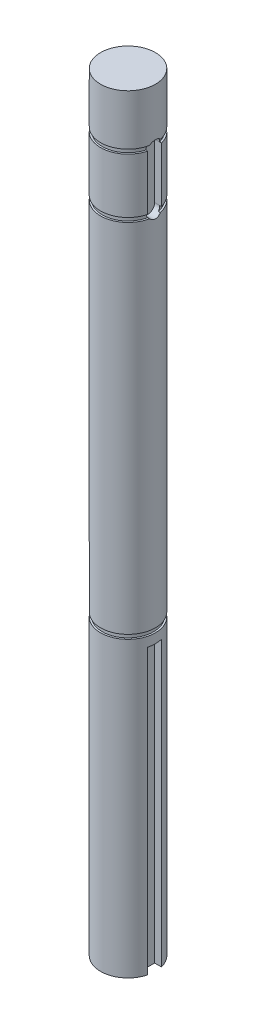
SolidWorks part; units mm, degrees
material "AISI 1020"
ref_plane "Front Plane" through (0, 0, 0) normal (0, 0, 1) x (1, 0, 0)
ref_plane "Top Plane" through (0, 0, 0) normal (0, 1, 0) x (1, 0, 0)
ref_plane "Right Plane" through (0, 0, 0) normal (1, 0, 0) x (0, 0, -1)
sketch "Sketch1" plane through (0, 0, 0) normal (0, 1, 0) x (1, 0, 0)
  circle A0 centre (0, 0) radius 6.35
extrude "Boss-Extrude1" add sketch "Sketch1" along normal blind 177.8 contours A0
sketch "Sketch2" plane through (0, 0, 0) normal (1, 0, 0) x (0, 0, -1)
  line L0 (6.35, 177.8) -> (-6.35, 177.8) construction
  line L1 (-44.9225, 166.0906) -> (-5.9436, 166.0906)
  line L2 (-44.9225, 166.0906) -> (-44.9225, 165.1)
  line L3 (-44.9225, 165.1) -> (-5.9436, 165.1)
  line L4 (-5.9436, 166.0906) -> (-5.9436, 165.1)
  line L5 (-6.35, 177.8) -> (-6.35, 0) construction
  line L6 (0, 174.6641) -> (0, 151.3771) construction
  dimension "D1" = 11.7094
  dimension "D2" = 0.9906
  dimension "D3" = 0.4064
revolve "Cut-Revolve1" cut sketch "Sketch2" angle 360 about L6
sketch "Sketch3" plane through (0, 0, 0) normal (1, 0, 0) x (0, 0, -1)
  line L0 (6.35, 165.1) -> (-6.35, 165.1) construction
  line L1 (-32.0705, 152.4) -> (-5.9436, 152.4)
  line L2 (-32.0705, 152.4) -> (-32.0705, 151.4094)
  line L3 (-32.0705, 151.4094) -> (-5.9436, 151.4094)
  line L4 (-5.9436, 152.4) -> (-5.9436, 151.4094)
  line L5 (-6.35, 165.1) -> (-6.35, 0) construction
  line L6 (0, 162.0139) -> (0, 148.2711) construction
  dimension "D1" = 12.7
  dimension "D2" = 0.9906
  dimension "D3" = 0.4064
revolve "Cut-Revolve2" cut sketch "Sketch3" angle 360 about L6
sketch "Sketch4" plane through (0, 0, 0) normal (1, 0, 0) x (0, 0, -1)
  line L0 (6.35, 151.4094) -> (-6.35, 151.4094) construction
  line L1 (-51.9937, 68.8594) -> (-5.9436, 68.8594)
  line L2 (-51.9937, 68.8594) -> (-51.9937, 67.8688)
  line L3 (-51.9937, 67.8688) -> (-5.9436, 67.8688)
  line L4 (-5.9436, 68.8594) -> (-5.9436, 67.8688)
  line L5 (-6.35, 151.4094) -> (-6.35, 0) construction
  line L6 (0, 70.2954) -> (0, 64.126) construction
  dimension "D1" = 82.55
  dimension "D2" = 0.9906
  dimension "D3" = 0.4064
revolve "Cut-Revolve3" cut sketch "Sketch4" angle 360 about L6
ref_plane "Plane1" through (6.35, 0, 0) normal (1, 0, 0) x (0, 0, -1)
sketch "Sketch5" plane through (6.35, 0, 0) normal (1, 0, 0) x (0, 0, -1)
  line L0 (0, 165.1) -> (0, 152.4) construction
  line L1 (6.35, 165.1) -> (-6.35, 165.1) construction
  line L2 (-5.9436, 152.4) -> (5.9436, 152.4) construction
  line L3 (1.5875, 165.1) -> (1.5875, 152.4)
  line L4 (-1.5875, 165.1) -> (-1.5875, 152.4)
  arc A0 (1.5875, 165.1) -> (-1.5875, 165.1) centre (0, 165.1) ccw
  arc A1 (-1.5875, 152.4) -> (1.5875, 152.4) centre (0, 152.4) ccw
  point P6 (0, 158.75)
  dimension "D1" = 3.175
extrude "Cut-Extrude1" cut sketch "Sketch5" against normal blind 1.778 contours L4 A1 L3 A0
sketch "Sketch6" plane through (6.35, 0, 0) normal (1, 0, 0) x (0, 0, -1)
  line L0 (6.35, 67.8688) -> (-6.35, 67.8688) construction
  line L1 (-1.5875, 65.6844) -> (1.5875, 65.6844)
  line L2 (-1.5875, 65.6844) -> (-1.5875, -15.0822)
  line L3 (-1.5875, -15.0822) -> (1.5875, -15.0822)
  line L4 (1.5875, 65.6844) -> (1.5875, -15.0822)
  line L5 (6.35, 0) -> (6.35, 67.8688) construction
  dimension "D1" = 2.1844
  dimension "D2" = 4.7625
  dimension "D3" = 3.175
extrude "Cut-Extrude2" cut sketch "Sketch6" against normal blind 1.778
